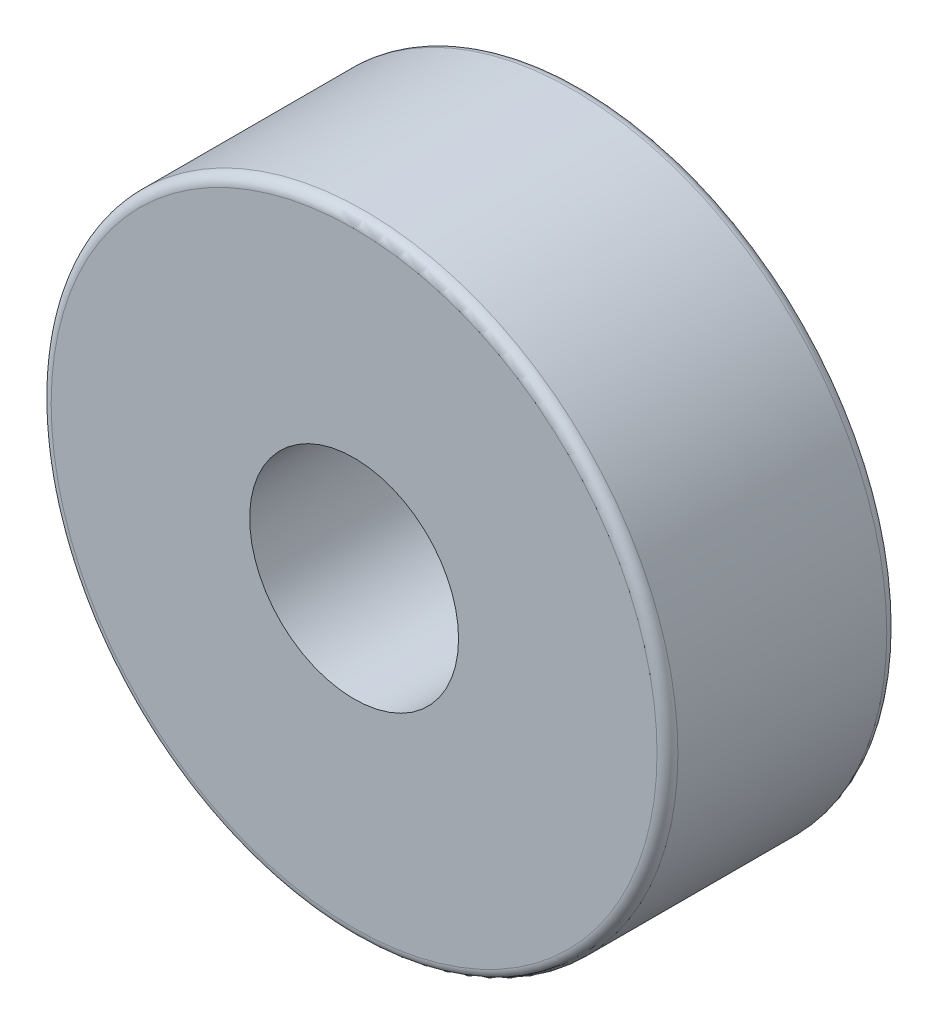
SolidWorks part; units mm, degrees
material "Alloy Steel (SS)"
ref_plane "Front Plane" through (0, 0, 0) normal (0, 0, 1) x (1, 0, 0)
ref_plane "Top Plane" through (0, 0, 0) normal (0, 1, 0) x (1, 0, 0)
ref_plane "Right Plane" through (0, 0, 0) normal (1, 0, 0) x (0, 0, -1)
sketch "Sketch1" plane through (0, 0, 0) normal (0, 0, 1) x (1, 0, 0)
  circle A0 centre (0, 0) radius 30
  dimension "D1" = 60
extrude "Boss-Extrude1" add sketch "Sketch1" along normal blind 22
sketch "Sketch2" plane through (0, 0, 0) normal (0, 0, -1) x (-1, 0, 0)
  circle A0 centre (0, 0) radius 10
  dimension "D1" = 20
extrude "Cut-Extrude1" cut sketch "Sketch2" against normal blind 66
fillet "Fillet1" radius 1 2 edges at (30, 0, 22) (30, 0, 0)
sketch "Sketch3" plane through (0, 0, 0) normal (0, 0, -1) x (-1, 0, 0)
  line L0 (-10.1504, 0) -> (10.0348, 0) construction
  line L1 (0, 9) -> (0, -11.8711) construction
  line L2 (-0.5, 24.995) -> (-0.5, 3.4641)
  line L3 (0.5, 24.995) -> (0.5, 3.4641)
  line L4 (-24.995, -0.5) -> (-3.4641, -0.5)
  line L5 (-24.995, 0.5) -> (-3.4641, 0.5)
  line L7 (-10.1504, 0.5) -> (10.0348, 0.5) construction
  line L8 (-10.1504, -0.5) -> (10.0348, -0.5) construction
  line L9 (0, 9.3552) -> (0, -11.8711) construction
  line L10 (-0.5, -3.4641) -> (-0.5, -24.995)
  line L11 (0.5, -3.4641) -> (0.5, -24.995)
  line L12 (-0.5, 9.3552) -> (-0.5, -11.8711) construction
  line L13 (3.4641, -0.5) -> (24.995, -0.5)
  line L14 (0.5, 9.3552) -> (0.5, -11.8711) construction
  line L15 (3.4641, 0.5) -> (24.995, 0.5)
  arc A0 (-3.4641, -0.5) -> (-0.5, -3.4641) centre (0, 0) ccw
  arc A1 (-0.5, 24.995) -> (-24.995, 0.5) centre (0, 0) ccw
  arc A2 (0.5, -3.4641) -> (3.4641, -0.5) centre (0, 0) ccw
  arc A3 (3.4641, 0.5) -> (0.5, 3.4641) centre (0, 0) ccw
  arc A4 (-0.5, 3.4641) -> (-3.4641, 0.5) centre (0, 0) ccw
  arc A5 (24.995, 0.5) -> (0.5, 24.995) centre (0, 0) ccw
  arc A6 (0.5, -24.995) -> (24.995, -0.5) centre (0, 0) ccw
  arc A7 (-24.995, -0.5) -> (-0.5, -24.995) centre (0, 0) ccw
  dimension "D1" = 7
  dimension "D2" = 50
  dimension "D7" = 0.5
  dimension "D8" = 0.5
  dimension "D3" = 0.5
  dimension "D4" = 0.5
  dimension "D5" = 0.5
  dimension "D6" = 0.5
extrude "Cut-Extrude2" cut sketch "Sketch3" against normal blind 2
sketch "Sketch4" plane through (0, 0, 0) normal (0, 0, -1) x (-1, 0, 0)
  line L0 (-27.3457, -30) -> (32.5969, -30) construction
  circle A0 centre (0, 0) radius 30 construction
  dimension "D1" = 30
